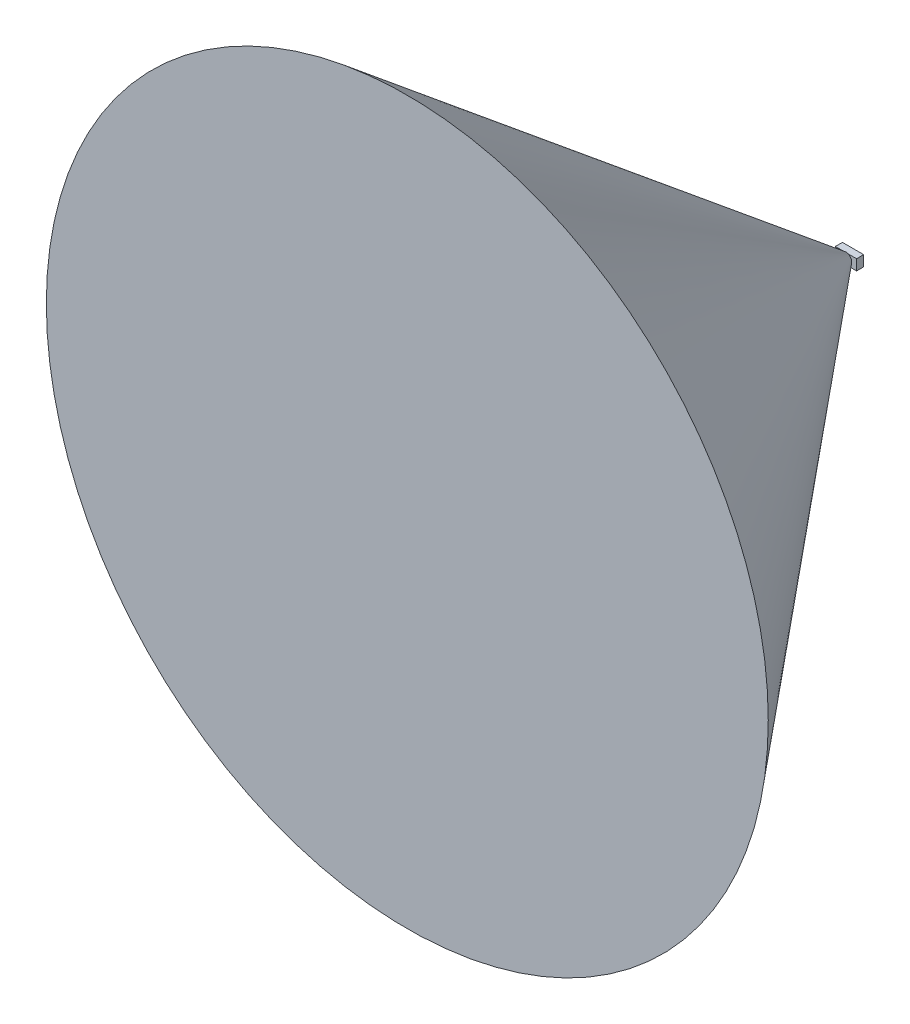
SolidWorks part; units mm, degrees
ref_plane "Front Plane" through (0, 0, 0) normal (0, 0, 1) x (1, 0, 0)
ref_plane "Top Plane" through (0, 0, 0) normal (0, 1, 0) x (1, 0, 0)
ref_plane "Right Plane" through (0, 0, 0) normal (1, 0, 0) x (0, 0, -1)
sketch "Sketch1" plane through (0, 0, 0) normal (0, 0, 1) x (1, 0, 0)
  line L1 (19.05, -9.525) -> (-19.05, -9.525)
  line L2 (19.05, -9.525) -> (19.05, 9.525)
  line L3 (19.05, 9.525) -> (-19.05, 9.525)
  line L4 (-19.05, -9.525) -> (-19.05, 9.525)
  line L5 (19.05, -9.525) -> (-19.05, 9.525) construction
  line L6 (19.05, 9.525) -> (-19.05, -9.525) construction
  point P0 (0, 0)
  dimension "D1" = 19.05
  dimension "D2" = 38.1
extrude "Boss-Extrude1" add sketch "Sketch1" along normal blind 12.7
sketch "Sketch2" plane through (0, 0, 0) normal (1, 0, 0) x (0, 0, -1)
  line L0 (0, 0) -> (-800, 647.8272)
  line L1 (-800, 647.8272) -> (-800, 0)
  line L2 (-800, 0) -> (0, 0)
  dimension "D1" = 800
  dimension "D2" = 39
revolve "Revolve1" add sketch "Sketch2" angle 360 about L2
